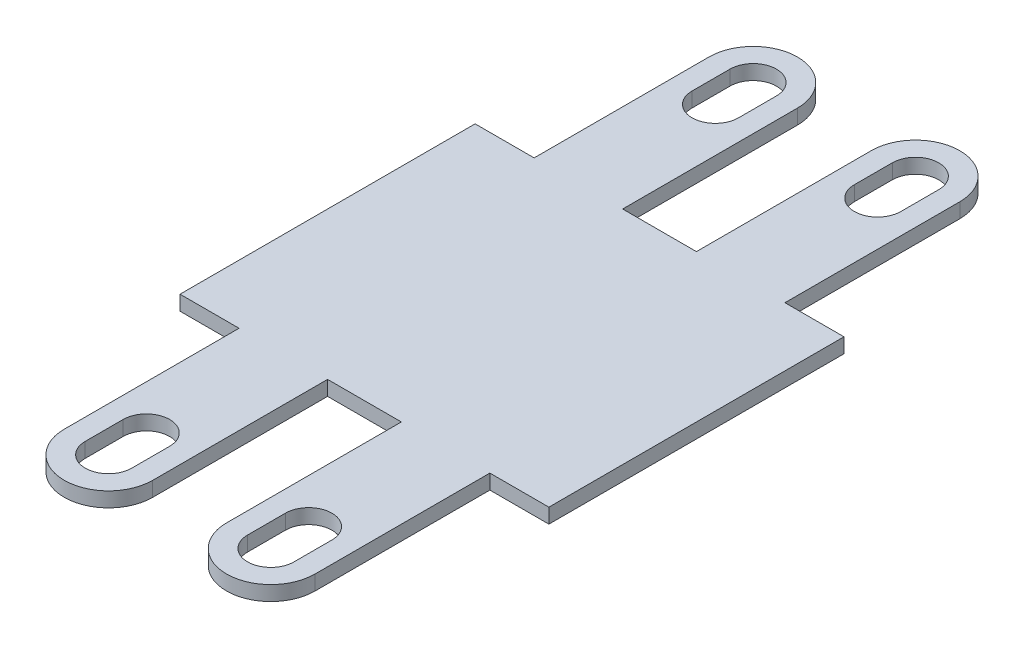
SolidWorks part; units mm, degrees
ref_plane "Front Plane" through (0, 0, 0) normal (0, 0, 1) x (1, 0, 0)
ref_plane "Top Plane" through (0, 0, 0) normal (0, 1, 0) x (1, 0, 0)
ref_plane "Right Plane" through (0, 0, 0) normal (1, 0, 0) x (0, 0, -1)
sketch "Sketch1" plane through (0, 0, 0) normal (0, 1, 0) x (1, 0, 0)
  line L0 (-9.3353, 23.97) -> (-9.3353, 47.67) construction
  line L1 (-23.3353, 23.97) -> (-15.3353, 23.97)
  line L2 (-23.3353, 23.97) -> (-23.3353, -16.03)
  line L3 (-9.3353, -39.73) -> (-9.3353, -16.03) construction
  line L4 (26.6647, 23.97) -> (26.6647, -16.03)
  line L5 (-15.3353, 23.97) -> (-15.3353, 47.67)
  line L6 (-3.3353, 23.97) -> (-3.3353, 47.67)
  line L7 (1.6647, 23.9449) -> (1.6647, 3.9449) construction
  line L8 (18.6647, 23.97) -> (18.6647, 47.67)
  line L9 (-9.3353, 47.67) -> (-9.3353, 23.97) construction
  line L10 (-9.3353, 47.67) -> (-9.3353, 42.5295) construction
  line L11 (-23.3353, 3.97) -> (26.6647, 3.97) construction
  line L12 (-9.3353, -16.03) -> (-9.3353, -39.73) construction
  line L13 (12.6647, 47.67) -> (12.6647, 42.5295) construction
  line L14 (9.5147, 47.67) -> (9.5147, 42.5295)
  line L15 (-6.1853, 47.67) -> (-6.1853, 42.5295)
  line L16 (15.8147, 47.67) -> (15.8147, 42.5295)
  line L17 (6.6647, 23.97) -> (6.6647, 47.67)
  line L18 (-3.3353, 23.97) -> (6.6647, 23.97)
  line L19 (-12.4853, 47.67) -> (-12.4853, 42.5295)
  line L20 (18.6647, -16.03) -> (26.6647, -16.03)
  line L21 (-3.3353, -16.03) -> (6.6647, -16.03)
  line L22 (6.6647, -16.03) -> (6.6647, -39.73)
  line L23 (18.6647, -16.03) -> (18.6647, -39.73)
  line L24 (-3.3353, -16.03) -> (-3.3353, -39.73)
  line L25 (-15.3353, -16.03) -> (-15.3353, -39.73)
  line L26 (-23.3353, -16.03) -> (-15.3353, -16.03)
  line L27 (12.6647, -39.73) -> (12.6647, -34.5894) construction
  line L28 (9.5147, -39.73) -> (9.5147, -34.5894)
  line L29 (15.8147, -39.73) -> (15.8147, -34.5894)
  line L30 (-9.3353, -39.73) -> (-9.3353, -34.5894) construction
  line L31 (18.6647, 23.97) -> (26.6647, 23.97)
  line L32 (-6.1853, -39.73) -> (-6.1853, -34.5894)
  line L33 (-12.4853, -39.73) -> (-12.4853, -34.5894)
  arc A0 (9.5147, 47.67) -> (15.8147, 47.67) centre (12.6647, 47.67) cw
  arc A1 (-3.3353, 47.67) -> (-15.3353, 47.67) centre (-9.3353, 47.67) ccw
  arc A2 (-6.1853, 47.67) -> (-12.4853, 47.67) centre (-9.3353, 47.67) ccw
  arc A3 (-12.4853, 42.5295) -> (-6.1853, 42.5295) centre (-9.3353, 42.5295) ccw
  arc A4 (15.8147, 42.5295) -> (9.5147, 42.5295) centre (12.6647, 42.5295) cw
  arc A5 (6.6647, 47.67) -> (18.6647, 47.67) centre (12.6647, 47.67) cw
  arc A6 (6.6647, -39.73) -> (18.6647, -39.73) centre (12.6647, -39.73) ccw
  arc A7 (-3.3353, -39.73) -> (-15.3353, -39.73) centre (-9.3353, -39.73) cw
  arc A8 (9.5147, -39.73) -> (15.8147, -39.73) centre (12.6647, -39.73) ccw
  arc A9 (15.8147, -34.5894) -> (9.5147, -34.5894) centre (12.6647, -34.5894) ccw
  arc A10 (-6.1853, -39.73) -> (-12.4853, -39.73) centre (-9.3353, -39.73) cw
  arc A11 (-12.4853, -34.5894) -> (-6.1853, -34.5894) centre (-9.3353, -34.5894) cw
  point P4 (-9.3353, 35.82)
  point P17 (-9.3353, 45.0998)
  point P24 (12.6647, 45.0998)
  point P45 (12.6647, -37.1597)
  point P51 (-9.3353, -37.1597)
  point P56 (-9.3353, -27.88)
  dimension "D3" = 23.7
  dimension "D4" = 11
  dimension "D5" = 25
  dimension "D1" = 50
  dimension "D2" = 40
extrude "Boss-Extrude1" add sketch "Sketch1" along normal blind 2
